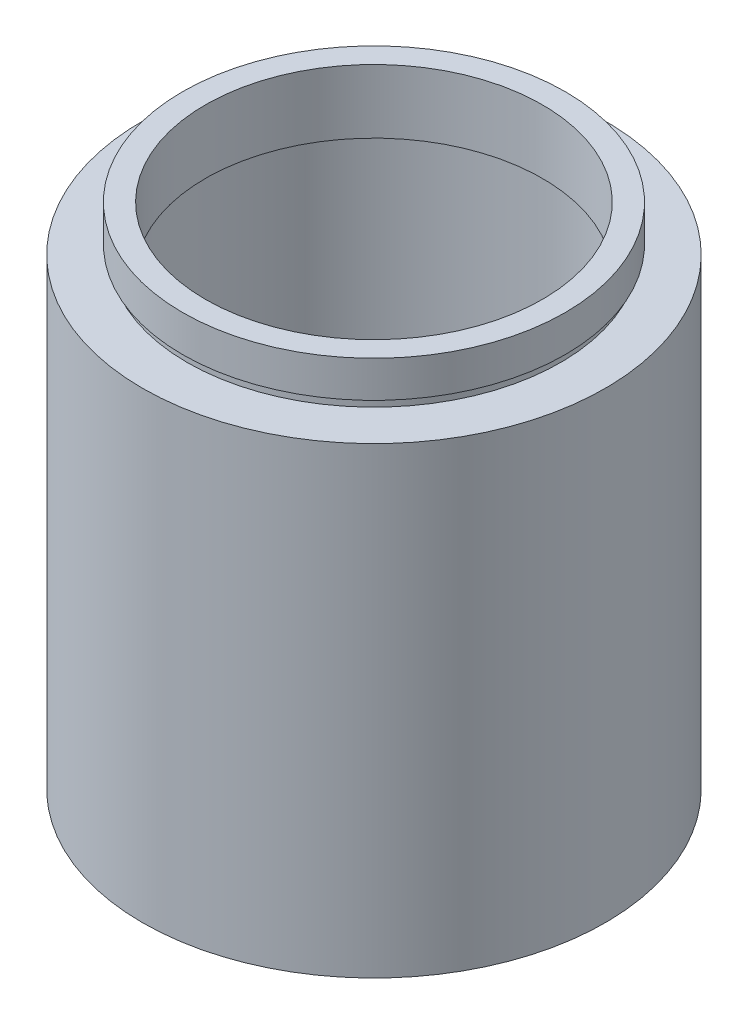
SolidWorks part; units mm, degrees
ref_plane "前视基准面" through (0, 0, 0) normal (0, 0, 1) x (1, 0, 0)
ref_plane "上视基准面" through (0, 0, 0) normal (0, 1, 0) x (1, 0, 0)
ref_plane "右视基准面" through (0, 0, 0) normal (1, 0, 0) x (0, 0, -1)
sketch "草图1" plane through (0, 0, 0) normal (0, 0, 1) x (1, 0, 0)
  line L0 (0, 161.3762) -> (0, 0) construction
  line L1 (141.7365, 0) -> (-131.7984, 0) construction
  line L2 (18.5, 55.8) -> (21, 55.8)
  line L3 (21, 55.8) -> (21, 51.8)
  line L4 (21, 51.8) -> (20.5, 51.8)
  line L5 (20.5, 51.8) -> (20.5, 50.8)
  line L6 (20.5, 50.8) -> (25.4, 50.8)
  line L7 (25.4, 50.8) -> (25.4, 0)
  line L8 (25.4, 0) -> (20.5, 0)
  line L9 (20.5, 0) -> (20.5, 47.8)
  line L10 (20.5, 47.8) -> (21.1, 47.8)
  line L11 (21.1, 47.8) -> (21.1, 48.8)
  line L12 (21.1, 48.8) -> (18.5, 48.8)
  line L13 (18.5, 48.8) -> (18.5, 55.8)
  dimension "D1" = 18.5
  dimension "D2" = 21
  dimension "D3" = 1
  dimension "D4" = 1
  dimension "D5" = 20.5
  dimension "D6" = 21.1
  dimension "D7" = 20.5
  dimension "D8" = 5
  dimension "D9" = 7
  dimension "D10" = 50.8
  dimension "D11" = 25.4
revolve "旋转1" add sketch "草图1" angle 360 about L0
cosmetic thread "装饰螺纹线1" parameters "D2"=42
cosmetic thread "装饰螺纹线2" parameters "D2"=38
cosmetic thread "装饰螺纹线3" parameters "D2"=41
